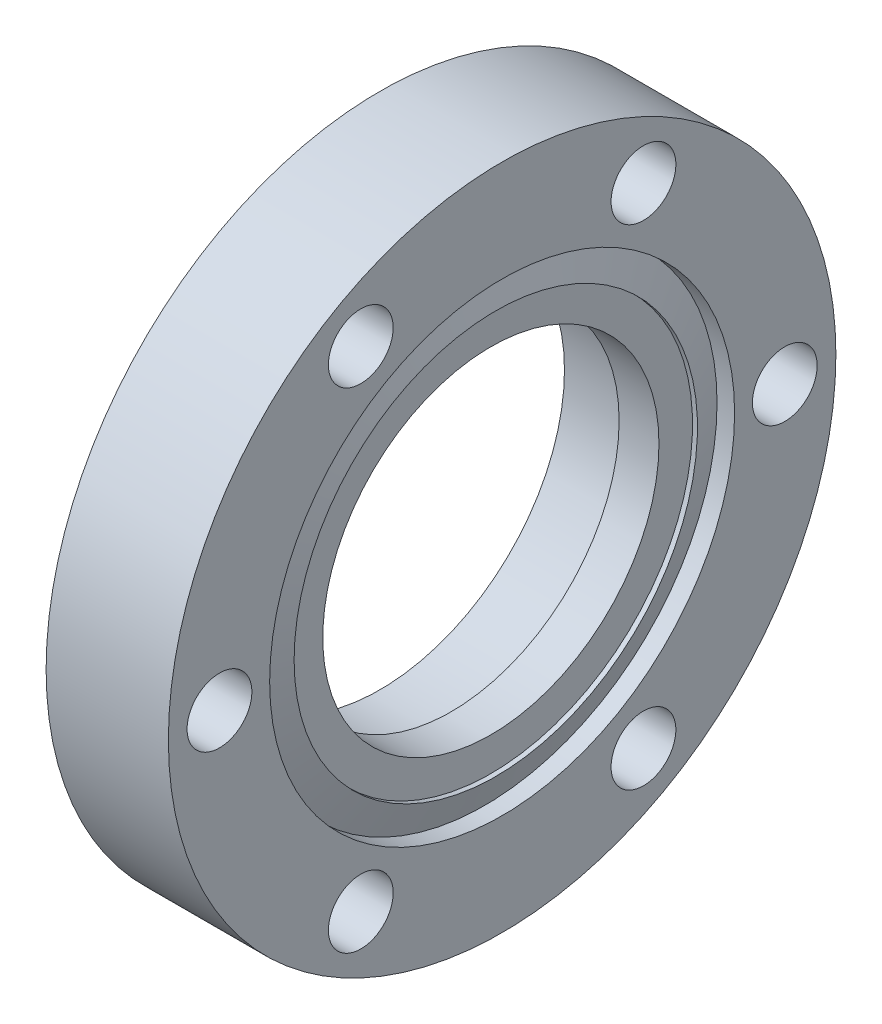
SolidWorks part; units mm, degrees
ref_plane "Front Plane" through (0, 0, 0) normal (0, 0, 1) x (1, 0, 0)
ref_plane "Top Plane" through (0, 0, 0) normal (0, 1, 0) x (1, 0, 0)
ref_plane "Right Plane" through (0, 0, 0) normal (1, 0, 0) x (0, 0, -1)
ref_plane "Plane4" through (0, 0, 0) normal (0, 0, -1) x (-1, 0, 0)
sketch "Sketch1" plane through (0, 0, 0) normal (0, 0, -1) x (-1, 0, 0)
  line L0 (-5.18, 20.95) -> (-5.18, 0)
  line L1 (-5.18, 0) -> (6.35, 0)
  line L2 (6.35, 0) -> (6.35, 34.671)
  line L3 (6.35, 34.671) -> (-6.35, 34.671)
  line L4 (-6.35, 34.671) -> (-6.35, 24.15)
  line L5 (-6.35, 24.15) -> (-4.5253, 24.15)
  line L6 (-4.5253, 24.15) -> (-5.69, 20.95)
  line L7 (-5.69, 20.95) -> (-5.18, 20.95)
  line L8 (-6.35, 0) -> (6.35, 0) construction
revolve "Revolve1" add sketch "Sketch1" angle 360 about L8
hole_wizard "1-3/8-6 Tapped Hole1" positions "Sketch3" profile "Sketch2" tap size "1-3/8-6" standard "ANSI Inch"
sketch "Sketch3" plane through (5.18, 0, 0) normal (1, 0, 0) x (0, 0, -1)
  point P0 (0, 0)
sketch "Sketch2" plane through (5.18, 0, 0) normal (0, 1, 0) x (0, 0, -1)
  line L0 (0, 0) -> (0, 11.53)
  line L1 (0, 11.53) -> (19.177, 11.53)
  line L2 (19.177, 11.53) -> (19.177, 4.1386)
  line L3 (19.177, 4.1386) -> (17.4625, 4.1386)
  line L4 (17.4625, 4.1386) -> (17.4625, 0)
  line L5 (17.4625, 0) -> (0, 0)
  line L10 (0, 11.53) -> (-19.177, 11.53) construction
  line L11 (0, -6.35) -> (0, 107.95) construction
  dimension "Tap Drill Dia." = 38.354
  dimension "Tap Drill Depth" = 11.53
  dimension "Thread Major Dia." = 34.925
  dimension "Thread Depth" = 4.1386
  dimension "Drill Angle" = 180
hole_wizard "1/4 Clearance Hole1" positions "Sketch5" profile "Sketch4" hole size "1/4" standard "ANSI Inch"
sketch "Sketch5" plane through (-6.35, 0, 0) normal (-1, 0, 0) x (0, 0, 1)
  point P0 (14.6812, -25.4286)
  point P1 (29.3624, 0)
  point P2 (14.6812, 25.4286)
  point P3 (-14.6812, 25.4286)
  point P4 (-14.6812, -25.4286)
  point P5 (-29.3624, 0)
sketch "Sketch4" plane through (-6.35, -25.4286, 14.6812) normal (0, 1, 0) x (0, 0, 1)
  line L0 (0, 0) -> (0, 12.7)
  line L1 (0, 12.7) -> (3.3655, 12.7)
  line L2 (3.3655, 12.7) -> (3.3655, 0)
  line L5 (3.3655, 0) -> (0, 0)
  line L11 (0, -6.35) -> (0, 107.95) construction
  dimension "Thru Hole Dia." = 6.731
  dimension "Thru Hole Depth" = 12.7
